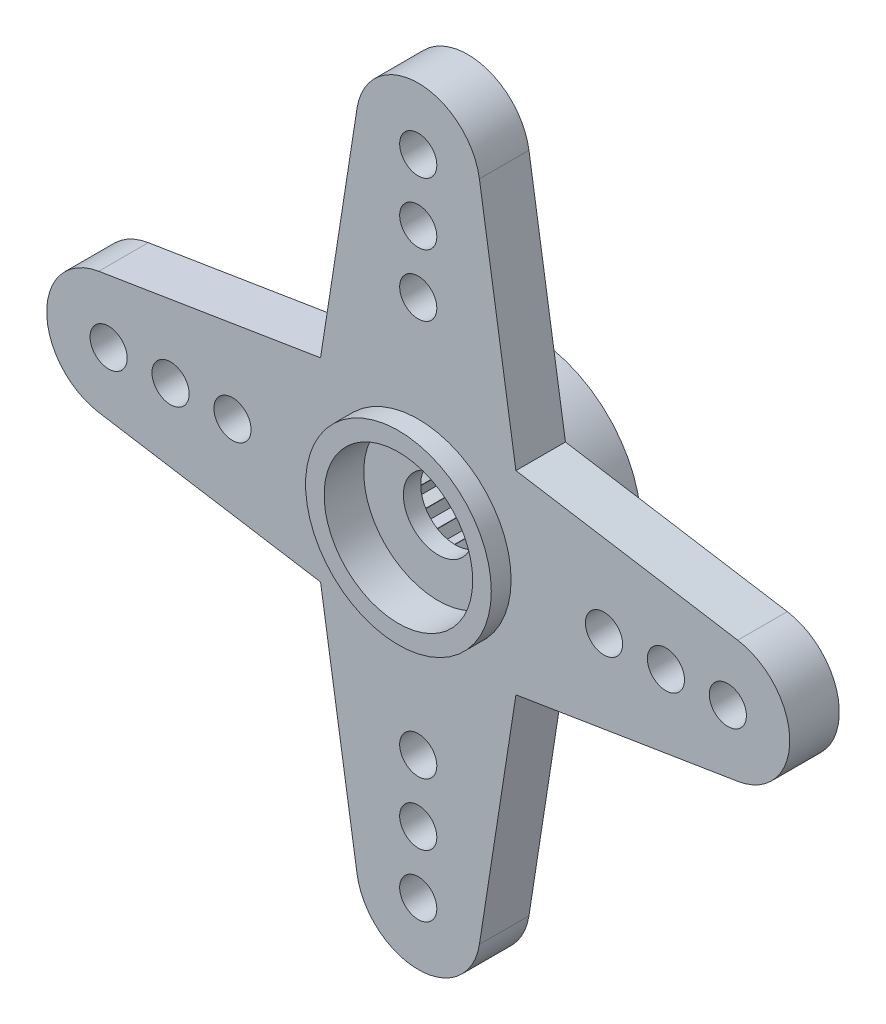
SolidWorks part; units mm, degrees
ref_plane "Face" through (0, 0, 0) normal (0, 0, 1) x (1, 0, 0)
ref_plane "Dessus" through (0, 0, 0) normal (0, 1, 0) x (1, 0, 0)
ref_plane "Droite" through (0, 0, 0) normal (1, 0, 0) x (0, 0, -1)
sketch "Esquisse1" plane through (0, 0, 0) normal (0, 0, 1) x (1, 0, 0)
  circle A0 centre (0, 0) radius 4.5
  line B0 (2.0116, -1.5509) -> (2.0116, -2.0116)
  line B1 (0.3258, 2.519) -> (0, 2.8448)
  line B2 (0.3373, 2.5175) -> (0.3258, 2.519)
  line B3 (0.7363, 2.7479) -> (0.3373, 2.5175)
  line B4 (0.9666, 2.3489) -> (0.7363, 2.7479)
  line B5 (0.9774, 2.3444) -> (0.9666, 2.3489)
  line B6 (1.4224, 2.4637) -> (0.9774, 2.3444)
  line B7 (1.5416, 2.0186) -> (1.4224, 2.4637)
  line B8 (1.5509, 2.0116) -> (1.5416, 2.0186)
  line B9 (2.0116, 2.0116) -> (1.5509, 2.0116)
  line B10 (2.0116, 1.5509) -> (2.0116, 2.0116)
  line B11 (2.0186, 1.5416) -> (2.0116, 1.5509)
  line B12 (2.4637, 1.4224) -> (2.0186, 1.5416)
  line B13 (2.3444, 0.9774) -> (2.4637, 1.4224)
  line B14 (2.3489, 0.9666) -> (2.3444, 0.9774)
  line B15 (2.7479, 0.7363) -> (2.3489, 0.9666)
  line B16 (2.5175, 0.3373) -> (2.7479, 0.7363)
  line B17 (2.519, 0.3258) -> (2.5175, 0.3373)
  line B18 (2.8448, 0) -> (2.519, 0.3258)
  line B19 (2.519, -0.3258) -> (2.8448, 0)
  line B20 (2.5175, -0.3373) -> (2.519, -0.3258)
  line B21 (2.7479, -0.7363) -> (2.5175, -0.3373)
  line B22 (2.3489, -0.9666) -> (2.7479, -0.7363)
  line B23 (2.3444, -0.9774) -> (2.3489, -0.9666)
  line B24 (2.4637, -1.4224) -> (2.3444, -0.9774)
  line B25 (2.0186, -1.5416) -> (2.4637, -1.4224)
  line B26 (2.0116, -1.5509) -> (2.0186, -1.5416)
  line B27 (1.5509, -2.0116) -> (2.0116, -2.0116)
  line B28 (1.5416, -2.0186) -> (1.5509, -2.0116)
  line B29 (1.4224, -2.4637) -> (1.5416, -2.0186)
  line B30 (0.9774, -2.3444) -> (1.4224, -2.4637)
  line B31 (0.9666, -2.3489) -> (0.9774, -2.3444)
  line B32 (0.7363, -2.7479) -> (0.9666, -2.3489)
  line B33 (0.3373, -2.5175) -> (0.7363, -2.7479)
  line B34 (0.3258, -2.519) -> (0.3373, -2.5175)
  line B35 (0, -2.8448) -> (0.3258, -2.519)
  line B36 (-0.3258, -2.519) -> (0, -2.8448)
  line B37 (-0.3373, -2.5175) -> (-0.3258, -2.519)
  line B38 (-0.7363, -2.7479) -> (-0.3373, -2.5175)
  line B39 (-0.9666, -2.3489) -> (-0.7363, -2.7479)
  line B40 (-0.9774, -2.3444) -> (-0.9666, -2.3489)
  line B41 (-1.4224, -2.4637) -> (-0.9774, -2.3444)
  line B42 (-1.5416, -2.0186) -> (-1.4224, -2.4637)
  line B43 (-1.5509, -2.0116) -> (-1.5416, -2.0186)
  line B44 (-2.0116, -2.0116) -> (-1.5509, -2.0116)
  line B45 (-2.0116, -1.5509) -> (-2.0116, -2.0116)
  line B46 (-2.0186, -1.5416) -> (-2.0116, -1.5509)
  line B47 (-2.4637, -1.4224) -> (-2.0186, -1.5416)
  line B48 (-2.3444, -0.9774) -> (-2.4637, -1.4224)
  line B49 (-2.3489, -0.9666) -> (-2.3444, -0.9774)
  line B50 (-2.7479, -0.7363) -> (-2.3489, -0.9666)
  line B51 (-2.5175, -0.3373) -> (-2.7479, -0.7363)
  line B52 (-2.519, -0.3258) -> (-2.5175, -0.3373)
  line B53 (-2.8448, 0) -> (-2.519, -0.3258)
  line B54 (-2.519, 0.3258) -> (-2.8448, 0)
  line B55 (-2.5175, 0.3373) -> (-2.519, 0.3258)
  line B56 (-2.7479, 0.7363) -> (-2.5175, 0.3373)
  line B57 (-2.3489, 0.9666) -> (-2.7479, 0.7363)
  line B58 (-2.3444, 0.9774) -> (-2.3489, 0.9666)
  line B59 (-2.4637, 1.4224) -> (-2.3444, 0.9774)
  line B60 (-2.0186, 1.5416) -> (-2.4637, 1.4224)
  line B61 (-2.0116, 1.5509) -> (-2.0186, 1.5416)
  line B62 (-2.0116, 2.0116) -> (-2.0116, 1.5509)
  line B63 (-1.5509, 2.0116) -> (-2.0116, 2.0116)
  line B64 (-1.5416, 2.0186) -> (-1.5509, 2.0116)
  line B65 (-1.4224, 2.4637) -> (-1.5416, 2.0186)
  line B66 (-0.9774, 2.3444) -> (-1.4224, 2.4637)
  line B67 (-0.9666, 2.3489) -> (-0.9774, 2.3444)
  line B68 (-0.7363, 2.7479) -> (-0.9666, 2.3489)
  line B69 (-0.3373, 2.5175) -> (-0.7363, 2.7479)
  line B70 (-0.3258, 2.519) -> (-0.3373, 2.5175)
  line B71 (0, 2.8448) -> (-0.3258, 2.519)
  dimension "D1" = 9
sketch_block_instance "Block1-1"
sketch_block "Block1"
extrude "Boss.-Extru.1" add sketch "Esquisse1" along normal blind 3
sketch "Esquisse2" plane through (0, 0, 3) normal (0, 0, 1) x (1, 0, 0)
  line L0 (-12.9, 2.4678) -> (-0.72, 4.442)
  line L1 (-12.9, -2.4678) -> (-0.72, -4.442)
  arc A0 (-12.9, 2.4678) -> (-12.9, -2.4678) centre (-12.5, 0) ccw
  circle A1 centre (0, 0) radius 4.5 construction
  arc A2 (-0.72, 4.442) -> (-0.72, -4.442) centre (0, 0) ccw
  circle A3 centre (-12.5, 0) radius 0.75
  circle A4 centre (-10, 0) radius 0.75
  circle A5 centre (-7.5, 0) radius 0.75
  point P13 (-9.9168, 0)
  dimension "D1" = 12.5
  dimension "D2" = 5
  dimension "D3" = 1.5
  dimension "D5" = 7.5
  dimension "D4" = 10
extrude "Boss.-Extru.2" add sketch "Esquisse2" along direction (0, 0, 1) on the side of the normal blind 1.5 and the other way blind 0.5
pattern_circular "Répétition circulaire1" count 2 over 360 about axis through (0, 0, 0) along (0, 0, 1) of "Boss.-Extru.2"
sketch "Esquisse3" plane through (0, 0, 4.5) normal (0, 0, 1) x (1, 0, 0)
  line L0 (4.4464, -0.6923) -> (2.4702, -13.3846)
  line L1 (-4.4464, -0.6923) -> (-2.4702, -13.3846)
  arc A0 (-2.4702, -13.3846) -> (2.4702, -13.3846) centre (0, -13) ccw
  circle A1 centre (0, 0) radius 4.5 construction
  arc A2 (-4.4464, -0.6923) -> (4.4464, -0.6923) centre (0, 0) ccw
  circle A3 centre (0, -13) radius 0.75
  circle A4 centre (0, -10.5) radius 0.75
  circle A5 centre (0, -8) radius 0.75
  dimension "D1" = 5
  dimension "D2" = 13
  dimension "D3" = 1.5
  dimension "D4" = 8
  dimension "D5" = 10.5
extrude "Boss.-Extru.3" add sketch "Esquisse3" against normal up to surface (2 mm away) up to face at (6.75, 0, 2.5)
pattern_circular "Répétition circulaire2" count 2 over 360 about axis through (0, 0, 0) along (0, 0, 1) of "Boss.-Extru.3"
sketch "Esquisse5" plane through (0, 0, 3) normal (0, 0, 1) x (1, 0, 0)
  circle A0 centre (0, 0) radius 1.4
  circle A1 centre (0, 0) radius 4.5 construction
  circle A2 centre (0, 0) radius 4.5
  dimension "D1" = 2.8
extrude "Boss.-Extru.4" add sketch "Esquisse5" along normal blind 0.7
sketch "Esquisse6" plane through (0, 0, 3.7) normal (0, 0, 1) x (1, 0, 0)
  circle A0 centre (0, 0) radius 3
  circle A1 centre (0, 0) radius 4.5 construction
  circle A2 centre (0, 0) radius 4.5
  dimension "D1" = 6
extrude "Boss.-Extru.5" add sketch "Esquisse6" along normal up to surface (0.8 mm away)
sketch "Esquisse7" plane through (0, 0, 4.5) normal (0, 0, 1) x (1, 0, 0)
  circle A0 centre (0, 0) radius 3 construction
  circle A1 centre (0, 0) radius 3
  circle A2 centre (0, 0) radius 3.75
  dimension "D1" = 7.5
extrude "Boss.-Extru.6" add sketch "Esquisse7" along normal blind 0.8
